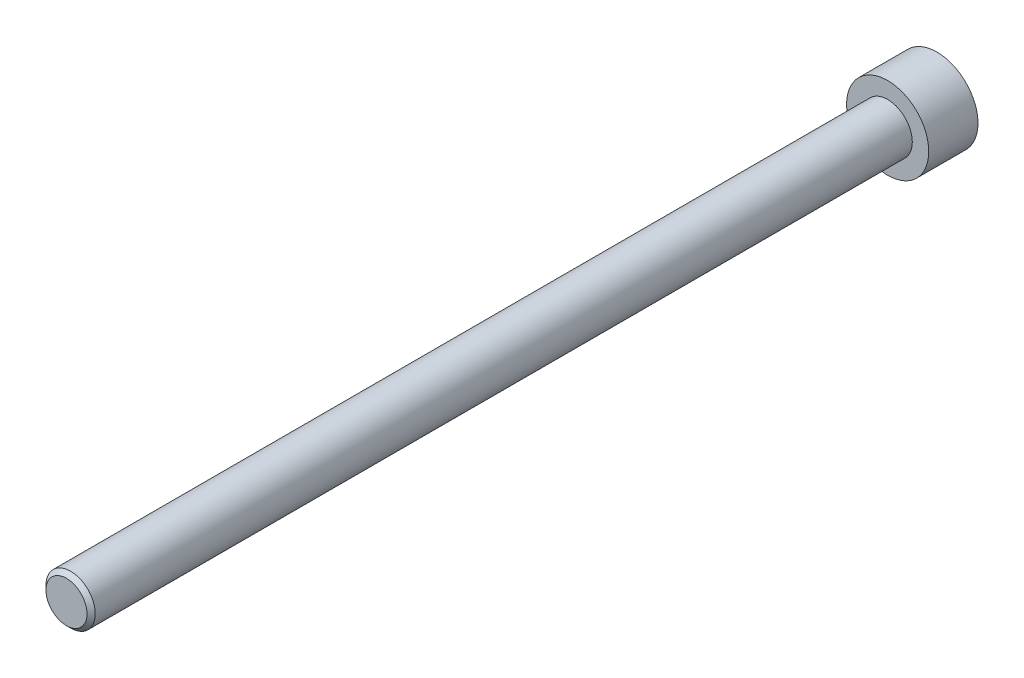
SolidWorks part; units mm, degrees
material "Acier allié inoxydable"
ref_plane "Plan de face" through (0, 0, 0) normal (0, 0, 1) x (1, 0, 0)
ref_plane "Plan de dessus" through (0, 0, 0) normal (0, 1, 0) x (1, 0, 0)
ref_plane "Plan de droite" through (0, 0, 0) normal (1, 0, 0) x (0, 0, -1)
sketch "Esquisse1" plane through (0, 0, 0) normal (0, 0, 1) x (1, 0, 0)
  circle A0 centre (0, 0) radius 5
  dimension "D1" = 10
extrude "Boss.-Extru.1" add sketch "Esquisse1" along normal blind 6
sketch "Esquisse2" plane through (0, 0, 6) normal (0, 0, 1) x (1, 0, 0)
  circle A0 centre (0, 0) radius 3
  dimension "D1" = 6
extrude "Boss.-Extru.2" add sketch "Esquisse2" along normal blind 100
chamfer "Chanfrein1" distance 0.5 angle 45 1 edges at (3, 0, 106)
sketch "Esquisse3" plane through (0, 0, 0) normal (0, 0, -1) x (-1, 0, 0)
  line L1 (-1.9388, -2.1388) -> (0.8828, -2.7484)
  line L2 (0.8828, -2.7484) -> (2.8216, -0.6097)
  line L3 (2.8216, -0.6097) -> (1.9388, 2.1388)
  line L4 (1.9388, 2.1388) -> (-0.8828, 2.7484)
  line L5 (-0.8828, 2.7484) -> (-2.8216, 0.6097)
  line L6 (-2.8216, 0.6097) -> (-1.9388, -2.1388)
  circle A0 centre (0, 0) radius 2.5 construction
  dimension "D1" = 5
extrude "Enlèv. mat.-Extru.1" cut sketch "Esquisse3" against normal blind 3.5
